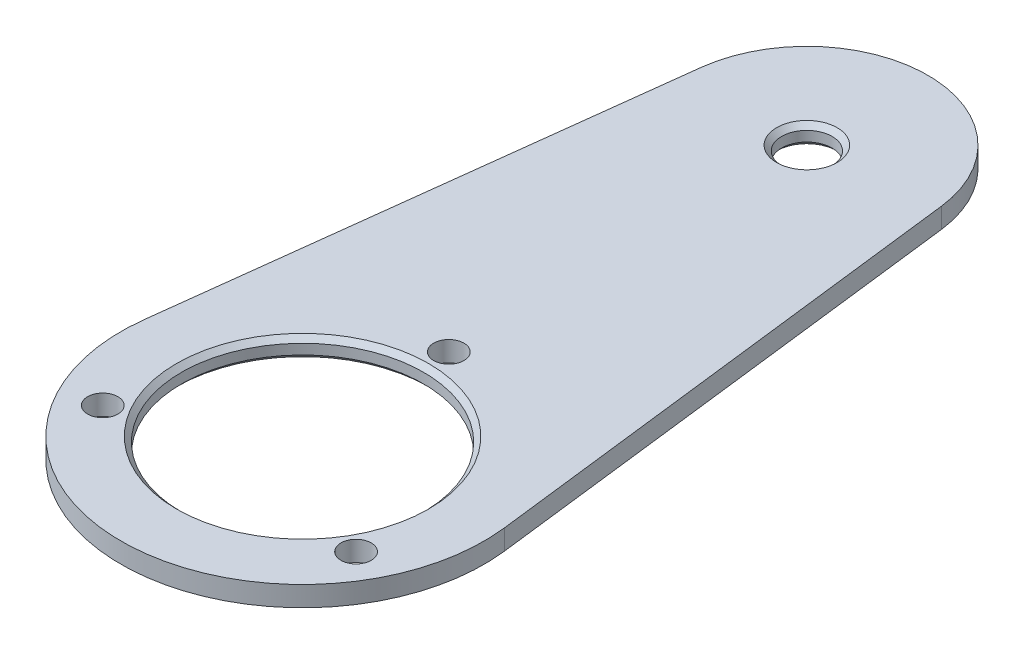
SolidWorks part; units mm, degrees
ref_plane "Face" through (0, 0, 0) normal (0, 0, 1) x (1, 0, 0)
ref_plane "Dessus" through (0, 0, 0) normal (0, 1, 0) x (1, 0, 0)
ref_plane "Droite" through (0, 0, 0) normal (1, 0, 0) x (0, 0, -1)
sketch "Esquisse1" plane through (0, 0, 0) normal (0, 1, 0) x (1, 0, 0)
  line L0 (0, 0) -> (0, 50) construction
  line L1 (-11.9133, 51.44) -> (-17.8699, 2.16)
  line L2 (11.9133, 51.44) -> (17.8699, 2.16)
  line L3 (0, 0) -> (15.5885, -9) construction
  line L4 (0, 0) -> (-15.5885, -9) construction
  arc A0 (-17.8699, 2.16) -> (17.8699, 2.16) centre (0, 0) ccw
  arc A1 (-11.9133, 51.44) -> (11.9133, 51.44) centre (0, 50) cw
  circle A2 centre (0, 0) radius 12
  circle A3 centre (0, 50) radius 2.5
  circle A4 centre (-12.5574, -7.25) radius 1.5
  circle A5 centre (12.5574, -7.25) radius 1.5
  circle A6 centre (0, 14.5) radius 1.5
  dimension "D1" = 18
  dimension "D3" = 24
  dimension "D4" = 5
  dimension "D5" = 12
  dimension "D8" = 3
  dimension "D2" = 50
  dimension "D6" = 120
  dimension "D7" = 120
  dimension "D9" = 14.5
  dimension "D10" = 14.5
  dimension "D11" = 14.5
extrude "Extrusion1" add sketch "Esquisse1" along normal blind 2
chamfer "Chanfrein1" distance 0.5 angle 45 4 edges at (0, 0, -47.5) (0, 2, -47.5) (0, 2, 12) (0, 0, 12)
